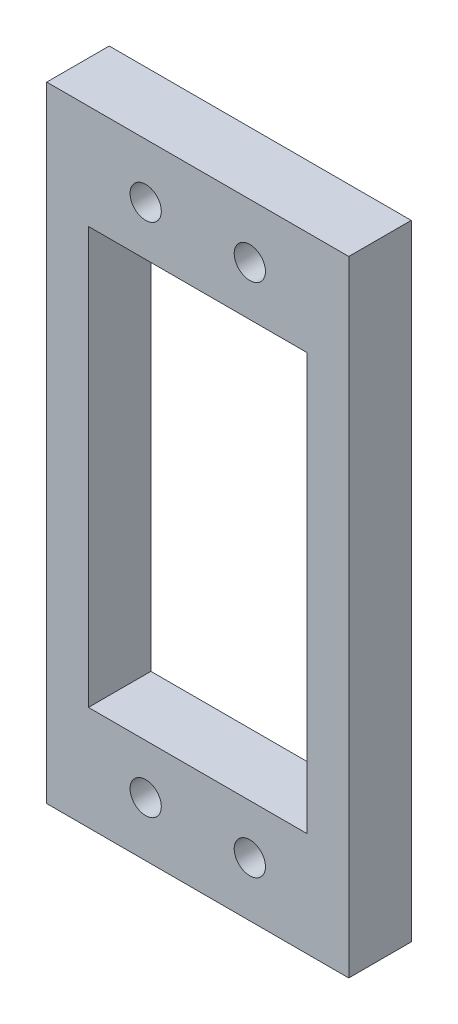
SolidWorks part; units mm, degrees
ref_plane "Plano frontal" through (0, 0, 0) normal (0, 0, 1) x (1, 0, 0)
ref_plane "Plano superior" through (0, 0, 0) normal (0, 1, 0) x (1, 0, 0)
ref_plane "Plano direito" through (0, 0, 0) normal (1, 0, 0) x (0, 0, -1)
sketch "Esboço1" plane through (0, 0, 0) normal (0, 0, 1) x (1, 0, 0)
  line L0 (0, 20) -> (0, 30) construction
  line L1 (-10.5, -20) -> (10.5, -20)
  line L2 (-10.5, -20) -> (-10.5, 20)
  line L3 (-10.5, 20) -> (10.5, 20)
  line L4 (10.5, -20) -> (10.5, 20)
  line L5 (-10.5, -20) -> (10.5, 20) construction
  line L6 (-10.5, 20) -> (10.5, -20) construction
  line L7 (-14.5, -30) -> (14.5, -30)
  line L8 (-14.5, -30) -> (-14.5, 30)
  line L9 (-14.5, 30) -> (14.5, 30)
  line L10 (14.5, -30) -> (14.5, 30)
  line L11 (-14.5, -30) -> (14.5, 30) construction
  line L12 (-14.5, 30) -> (14.5, -30) construction
  line L13 (10.5, 0) -> (14.5, 0) construction
  circle A0 centre (-5, 24.75) radius 1.5
  circle A1 centre (5, 24.75) radius 1.5
  circle A2 centre (5, -24.75) radius 1.5
  circle A3 centre (-5, -24.75) radius 1.5
  point P0 (0, 0)
  point P6 (0, 0)
  point P23 (16.1596, 28.8359)
  point P24 (11.4927, 20.508)
  dimension "D1" = 10
  dimension "D2" = 49.5
  dimension "D3" = 3
  dimension "D4" = 21
  dimension "D5" = 40
  dimension "D6" = 4
  dimension "D7" = 10
extrude "Ressalto-extrusão1" add sketch "Esboço1" along normal blind 6 contours L7 L10 L9 L8 A1 A0 L4 L1 L2 L3 A2 A3
